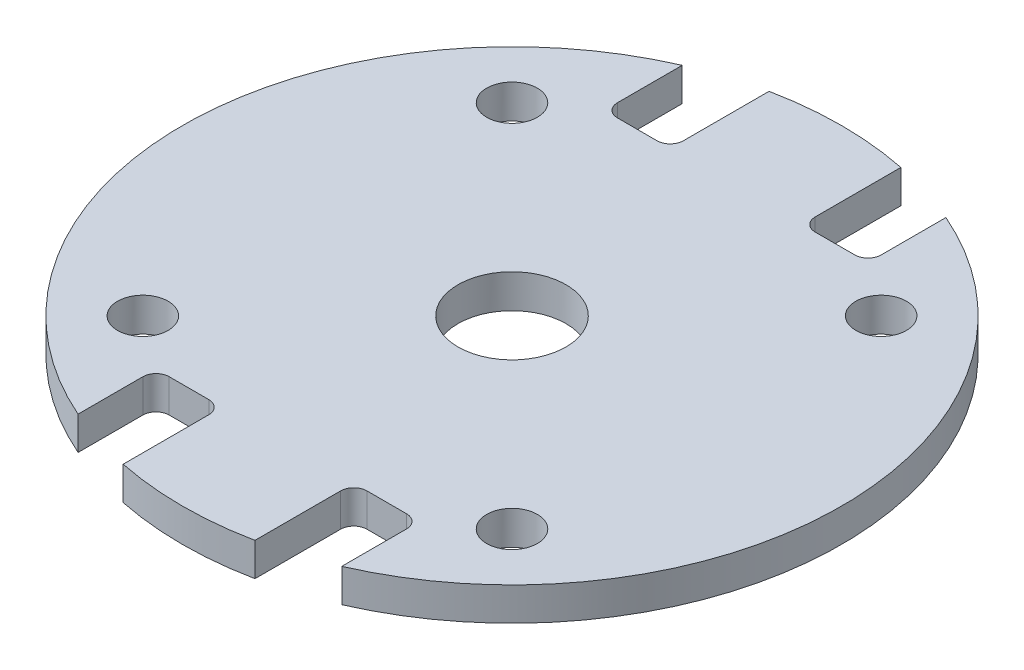
SolidWorks part; units mm, degrees
material "C110 COPPER"
ref_plane "Front Plane" through (0, 0, 0) normal (0, 0, 1) x (1, 0, 0)
ref_plane "Top Plane" through (0, 0, 0) normal (0, 1, 0) x (1, 0, 0)
ref_plane "Right Plane" through (0, 0, 0) normal (1, 0, 0) x (0, 0, -1)
sketch "Sketch1" plane through (0, 0, 0) normal (0, 1, 0) x (1, 0, 0)
  line L0 (0, 19.0669) -> (0, -19.7449) construction
  line L1 (-18.6997, 0) -> (19.2082, 0) construction
  line L2 (-6.35, 14.5497) -> (-6.35, 11.43)
  line L3 (-5.715, 10.795) -> (-3.81, 10.795)
  line L4 (-3.175, 11.43) -> (-3.175, 15.5543)
  line L5 (3.175, 11.43) -> (3.175, 15.5543)
  line L6 (5.715, 10.795) -> (3.81, 10.795)
  line L7 (6.35, 14.5497) -> (6.35, 11.43)
  line L8 (6.35, -14.5497) -> (6.35, -11.43)
  line L9 (5.715, -10.795) -> (3.81, -10.795)
  line L10 (3.175, -11.43) -> (3.175, -15.5543)
  line L11 (-3.175, -11.43) -> (-3.175, -15.5543)
  line L12 (-5.715, -10.795) -> (-3.81, -10.795)
  line L13 (-6.35, -14.5497) -> (-6.35, -11.43)
  arc A0 (-6.35, 14.5497) -> (-6.35, -14.5497) centre (0, 0) ccw
  arc A1 (-3.81, 10.795) -> (-3.175, 11.43) centre (-3.81, 11.43) ccw
  arc A2 (-6.35, 11.43) -> (-5.715, 10.795) centre (-5.715, 11.43) ccw
  arc A3 (6.35, 11.43) -> (5.715, 10.795) centre (5.715, 11.43) cw
  arc A4 (3.81, 10.795) -> (3.175, 11.43) centre (3.81, 11.43) cw
  arc A5 (3.81, -10.795) -> (3.175, -11.43) centre (3.81, -11.43) ccw
  arc A6 (6.35, -11.43) -> (5.715, -10.795) centre (5.715, -11.43) ccw
  arc A7 (-6.35, -11.43) -> (-5.715, -10.795) centre (-5.715, -11.43) cw
  arc A8 (-3.81, -10.795) -> (-3.175, -11.43) centre (-3.81, -11.43) cw
  arc A9 (3.175, 15.5543) -> (-3.175, 15.5543) centre (0, 0) ccw
  arc A10 (6.35, -14.5497) -> (6.35, 14.5497) centre (0, 0) ccw
  arc A11 (-3.175, -15.5543) -> (3.175, -15.5543) centre (0, 0) ccw
  dimension "D1" = 31.75
  dimension "D5" = 0.635
  dimension "D2" = 3.175
  dimension "D3" = 6.35
  dimension "D4" = 10.795
extrude "Boss-Extrude1" add sketch "Sketch1" along normal mid plane 1.6
sketch "Sketch4" plane through (0, 0.8, 0) normal (0, 1, 0) x (1, 0, 0)
  circle A0 centre (0, 0) radius 2.6
  dimension "D1" = 5.2
extrude "Cut-Extrude1" cut sketch "Sketch4" against normal through all
hole_wizard "#2 Clearance Hole1" positions "Sketch2" profile "Sketch3" hole size "#2" standard "ANSI Inch" end condition up to next
sketch "Sketch2" plane through (0, 0.8, 0) normal (0, 1, 0) x (1, 0, 0)
  line L1 (-8.89, 8.89) -> (8.89, 8.89)
  line L2 (-8.89, 8.89) -> (-8.89, -8.89)
  line L3 (-8.89, -8.89) -> (8.89, -8.89)
  line L4 (8.89, 8.89) -> (8.89, -8.89)
  line L5 (-8.89, 8.89) -> (8.89, -8.89) construction
  line L6 (-8.89, -8.89) -> (8.89, 8.89) construction
  point P0 (-8.89, 8.89)
  point P2 (8.89, 8.89)
  point P4 (-8.89, -8.89)
  point P6 (8.89, -8.89)
  point P63 (0, 0)
  dimension "D1" = 17.78
  dimension "D2" = 17.78
sketch "Sketch3" plane through (-8.89, 0.8, -8.89) normal (1, 0, 0) x (0, 0, 1)
  line L0 (0, 0) -> (0, 1.6)
  line L1 (0, 1.6) -> (1.2192, 1.6)
  line L2 (1.2192, 1.6) -> (1.2192, 0)
  line L5 (1.2192, 0) -> (0, 0)
  line L11 (0, -6.35) -> (0, 107.95) construction
  dimension "Thru Hole Dia." = 2.4384
  dimension "Thru Hole Depth" = 1.6
sketch "Sketch5" plane through (0, -0.8, 0) normal (0, -1, 0) x (1, 0, 0)
  circle A0 centre (-8.89, 8.89) radius 1.905
  circle A1 centre (8.89, 8.89) radius 1.905
  circle A2 centre (8.89, -8.89) radius 1.905
  circle A3 centre (-8.89, -8.89) radius 1.905
  circle A4 centre (0, 0) radius 3.81
  circle A5 centre (0, 0) radius 2.6 construction
  circle A6 centre (0, 0) radius 2.6
  circle A7 centre (-8.89, 8.89) radius 1.2192 construction
  circle A8 centre (-8.89, 8.89) radius 1.2192
  circle A9 centre (8.89, 8.89) radius 1.2192 construction
  circle A10 centre (8.89, 8.89) radius 1.2192
  circle A11 centre (8.89, -8.89) radius 1.2192 construction
  circle A12 centre (8.89, -8.89) radius 1.2192
  circle A13 centre (-8.89, -8.89) radius 1.2192 construction
  circle A14 centre (-8.89, -8.89) radius 1.2192
  dimension "D1" = 3.81
  dimension "D2" = 7.62
extrude "Boss-Extrude2" add sketch "Sketch5" along normal blind 0.0254
